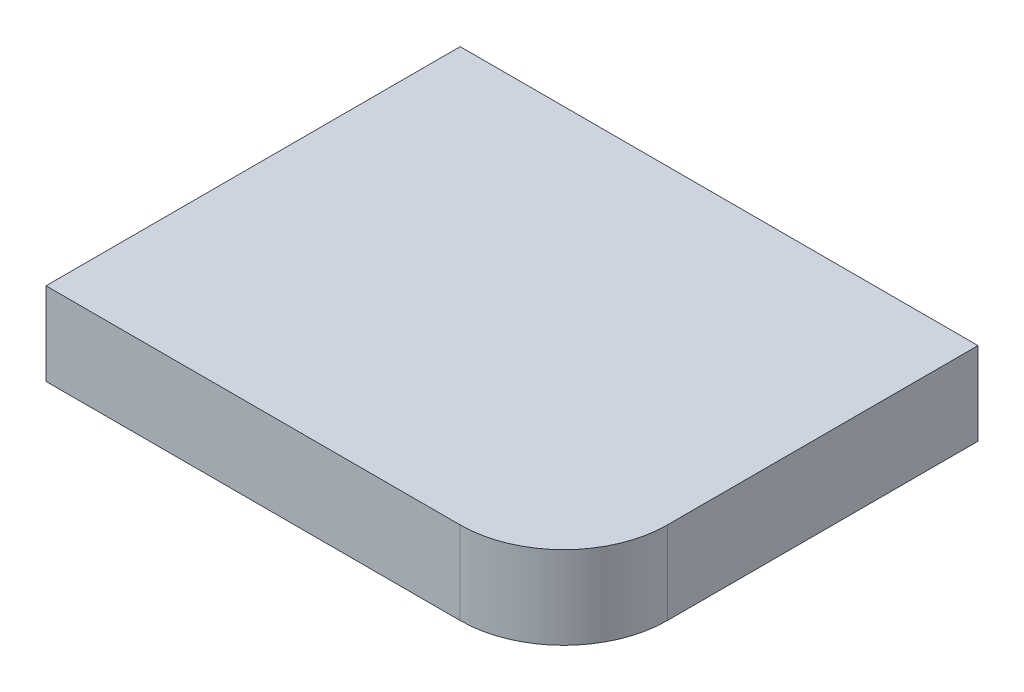
SolidWorks part; units mm, degrees
material "Клен"
ref_plane "Спереди" through (0, 0, 0) normal (0, 0, 1) x (1, 0, 0)
ref_plane "Сверху" through (0, 0, 0) normal (0, 1, 0) x (1, 0, 0)
ref_plane "Справа" through (0, 0, 0) normal (1, 0, 0) x (0, 0, -1)
sketch "Эскиз1" plane through (0, 0, 0) normal (0, 1, 0) x (1, 0, 0)
  line L1 (-25, -20) -> (15, -20)
  line L2 (-25, -20) -> (-25, 20)
  line L3 (-25, 20) -> (25, 20)
  line L4 (25, -10) -> (25, 20)
  line L5 (-25, -20) -> (25, 20) construction
  line L6 (-25, 20) -> (25, -20) construction
  arc A0 (15, -20) -> (25, -10) centre (15, -10) ccw
  point P0 (0, 0)
  dimension "D3" = 10
  dimension "D1" = 50
  dimension "D2" = 40
extrude "Бобышка-Вытянуть1" add sketch "Эскиз1" along normal blind 8
